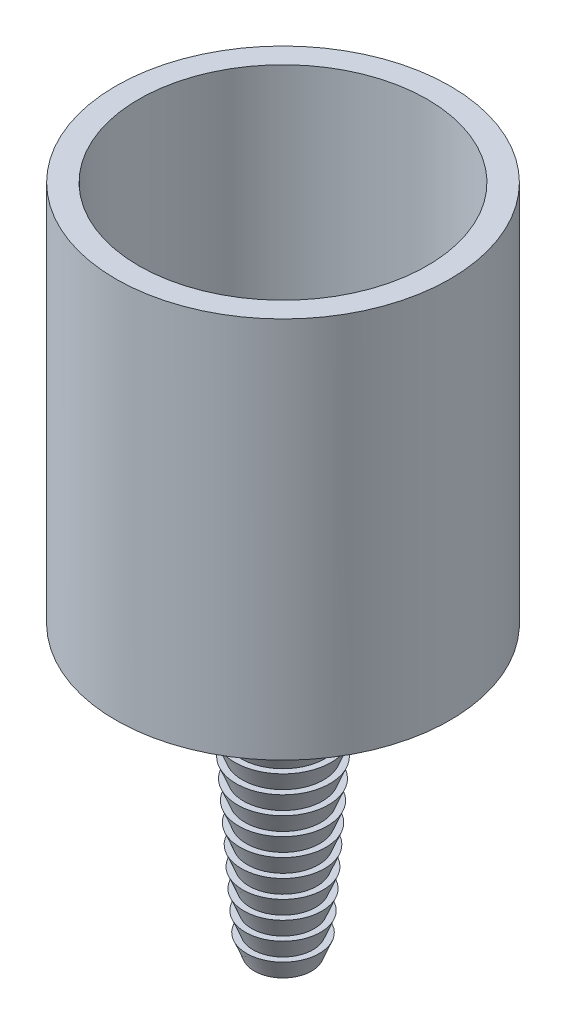
SolidWorks part; units mm, degrees
ref_plane "前视基准面" through (0, 0, 0) normal (0, 0, 1) x (1, 0, 0)
ref_plane "上视基准面" through (0, 0, 0) normal (0, 1, 0) x (1, 0, 0)
ref_plane "右视基准面" through (0, 0, 0) normal (1, 0, 0) x (0, 0, -1)
other "Configuration Table"
sketch "草图1" plane through (0, 0, 0) normal (0, 1, 0) x (1, 0, 0)
  circle A0 centre (0, 0) radius 17.5
  dimension "D1" = 35
extrude "凸台-拉伸1" add sketch "草图1" along normal blind 40
sketch "草图2" plane through (0, 40, 0) normal (0, 1, 0) x (1, 0, 0)
  circle A0 centre (0, 0) radius 15.1
  dimension "D1" = 30.2
extrude "切除-拉伸1" cut sketch "草图2" against normal blind 35
sketch "草图4" plane through (0, 0, 0) normal (0, 0, 1) x (1, 0, 0)
  line L0 (0, 0) -> (0, -30)
  line L1 (0, -30) -> (3, -30)
  line L2 (3, -30) -> (5.0978, 0) construction
  line L32 (3.8, -28) -> (3.1399, -28)
  line L33 (3.9395, -26.0049) -> (3.2794, -26.0049)
  line L34 (4.079, -24.0097) -> (3.4189, -24.0097)
  line L35 (4.2185, -22.0146) -> (3.5584, -22.0146)
  line L36 (4.3581, -20.0195) -> (3.6979, -20.0195)
  line L37 (4.4976, -18.0244) -> (3.8374, -18.0244)
  line L38 (4.6371, -16.0292) -> (3.9769, -16.0292)
  line L39 (4.7766, -14.0341) -> (4.1164, -14.0341)
  line L40 (4.9161, -12.039) -> (4.256, -12.039)
  line L41 (5.0556, -10.0438) -> (4.3955, -10.0438)
  line L42 (5.1951, -8.0487) -> (4.535, -8.0487)
  line L43 (5.3346, -6.0536) -> (4.6745, -6.0536)
  line L44 (5.4742, -4.0585) -> (4.814, -4.0585)
  line L45 (5.4742, -4.0585) -> (4.6745, -6.0536)
  line L46 (5.3346, -6.0536) -> (4.535, -8.0487)
  line L47 (5.1951, -8.0487) -> (4.3955, -10.0438)
  line L48 (5.0556, -10.0438) -> (4.256, -12.039)
  line L49 (4.9161, -12.039) -> (4.1164, -14.0341)
  line L50 (4.7766, -14.0341) -> (3.9769, -16.0292)
  line L51 (4.6371, -16.0292) -> (3.8374, -18.0244)
  line L52 (4.4976, -18.0244) -> (3.6979, -20.0195)
  line L53 (4.3581, -20.0195) -> (3.5584, -22.0146)
  line L54 (4.2185, -22.0146) -> (3.4189, -24.0097)
  line L55 (4.079, -24.0097) -> (3.2794, -26.0049)
  line L56 (3.9395, -26.0049) -> (3.1399, -28)
  line L57 (3.8, -28) -> (3, -30)
  line L58 (4.814, -4.0585) -> (17.5, 0)
  line L59 (17.5, 0) -> (0, 0)
  dimension "D1" = 4
revolve "旋转1" add sketch "草图4" angle 360 about L0
sketch "草图5" plane through (0, -30, 0) normal (0, -1, 0) x (1, 0, 0)
  circle A0 centre (0, 0) radius 1.75
  dimension "D1" = 3.5
extrude "切除-拉伸2" cut sketch "草图5" against normal through all
ref_plane "基准面2" through (0, 10, 0) normal (0, 1, 0) x (1, 0, 0)
sketch "草图8" plane through (0, 10, 0) normal (0, 1, 0) x (1, 0, 0)
  circle A0 centre (0, 0) radius 17.5
extrude "凸台-拉伸2" add sketch "草图8" along normal blind 5
sketch "草图11" plane through (0, 15, 0) normal (0, 1, 0) x (1, 0, 0)
  circle A0 centre (0, 0) radius 9 construction
  circle A1 centre (0, 0) radius 12.5 construction
  circle A2 centre (0, 9) radius 1
  circle A3 centre (3.6606, 8.2219) radius 1
  circle A4 centre (6.6883, 6.0222) radius 1
  circle A5 centre (8.5595, 2.7812) radius 1
  circle A6 centre (8.9507, -0.9408) radius 1
  circle A7 centre (7.7942, -4.5) radius 1
  circle A8 centre (5.2901, -7.2812) radius 1
  circle A9 centre (1.8712, -8.8033) radius 1
  circle A10 centre (-1.8712, -8.8033) radius 1
  circle A11 centre (-5.2901, -7.2812) radius 1
  circle A12 centre (-7.7942, -4.5) radius 1
  circle A13 centre (-8.9507, -0.9408) radius 1
  circle A14 centre (-8.5595, 2.7812) radius 1
  circle A15 centre (-6.6883, 6.0222) radius 1
  circle A16 centre (-3.6606, 8.2219) radius 1
  circle A27 centre (0, 12.5) radius 1
  circle A28 centre (3.1086, 12.1073) radius 1
  circle A29 centre (6.0219, 10.9538) radius 1
  circle A30 centre (8.5568, 9.1121) radius 1
  circle A31 centre (10.5541, 6.6978) radius 1
  circle A32 centre (11.8882, 3.8627) radius 1
  circle A33 centre (12.4753, 0.7849) radius 1
  circle A34 centre (12.2786, -2.3423) radius 1
  circle A35 centre (11.3103, -5.3222) radius 1
  circle A36 centre (9.6314, -7.9678) radius 1
  circle A37 centre (7.3473, -10.1127) radius 1
  circle A38 centre (4.6016, -11.6222) radius 1
  circle A39 centre (1.5667, -12.4014) radius 1
  circle A40 centre (-1.5667, -12.4014) radius 1
  circle A41 centre (-4.6016, -11.6222) radius 1
  circle A42 centre (-7.3473, -10.1127) radius 1
  circle A43 centre (-9.6314, -7.9678) radius 1
  circle A44 centre (-11.3103, -5.3222) radius 1
  circle A45 centre (-12.2786, -2.3423) radius 1
  circle A46 centre (-12.4753, 0.7849) radius 1
  circle A47 centre (-11.8882, 3.8627) radius 1
  circle A48 centre (-10.5541, 6.6978) radius 1
  circle A49 centre (-8.5568, 9.1121) radius 1
  circle A50 centre (-6.0219, 10.9538) radius 1
  circle A51 centre (-3.1086, 12.1073) radius 1
  point P56 (0, 0)
  point P137 (0, 0)
  dimension "D1" = 25
  dimension "D2" = 18
  dimension "D3" = 2
  dimension "D4" = 15
  dimension "D5" = 2
  dimension "D6" = 25
extrude "切除-拉伸3" cut sketch "草图11" against normal blind 5
